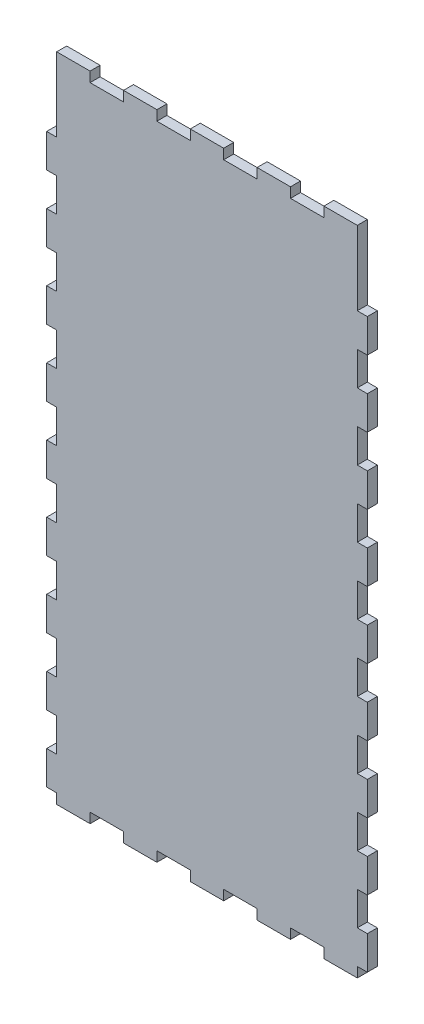
SolidWorks part; units mm, degrees
ref_plane "Plan de face" through (0, 0, 0) normal (0, 0, 1) x (1, 0, 0)
ref_plane "Plan de dessus" through (0, 0, 0) normal (0, 1, 0) x (1, 0, 0)
ref_plane "Plan de droite" through (0, 0, 0) normal (1, 0, 0) x (0, 0, -1)
sketch "Esquisse1" plane through (0, 0, 0) normal (0, 0, 1) x (1, 0, 0)
  line L1 (0, 0) -> (90, 0)
  line L2 (0, 0) -> (0, -189.15)
  line L3 (0, -189.15) -> (90, -189.15)
  line L4 (90, 0) -> (90, -189.15)
  dimension "D1" = 90
  dimension "D2" = 189.15
extrude "Boss.-Extru.1" add sketch "Esquisse1" along normal blind 3
sketch "Esquisse2" plane through (0, 0, 0) normal (0, 1, 0) x (1, 0, 0)
  line L0 (90, -3) -> (0, -3) construction
  line L1 (0, 0) -> (10, 0)
  line L2 (0, 0) -> (0, -3)
  line L3 (0, -3) -> (10, -3)
  line L4 (10, 0) -> (10, -3)
  dimension "D1" = 10
extrude "Boss.-Extru.2" add sketch "Esquisse2" along normal blind 3
pattern_linear "Répétition linéaire1" count 5 spacing 20 along (1, 0, 0) of "Boss.-Extru.2"
sketch "Esquisse3" plane through (0, -189.15, 0) normal (0, -1, 0) x (1, 0, 0)
  line L0 (0, 0) -> (90, 0) construction
  line L1 (0, 3) -> (10, 3)
  line L2 (0, 3) -> (0, 0)
  line L3 (0, 0) -> (10, 0)
  line L4 (10, 3) -> (10, 0)
  dimension "D1" = 10
extrude "Boss.-Extru.3" add sketch "Esquisse3" along normal blind 3
pattern_linear "Répétition linéaire2" count 5 spacing 20 along (1, 0, 0) of "Boss.-Extru.3"
sketch "Esquisse4" plane through (0, 0, 0) normal (-1, 0, 0) x (0, 0, 1)
  line L0 (3, 3) -> (3, -192.15) construction
  line L1 (3, -179.15) -> (0, -179.15)
  line L2 (3, -179.15) -> (3, -189.15)
  line L3 (3, -189.15) -> (0, -189.15)
  line L4 (0, -179.15) -> (0, -189.15)
  line L5 (0, 3) -> (0, -192.15) construction
  line L7 (3, -192.15) -> (0, -192.15) construction
  dimension "D1" = 10
  dimension "D2" = 3
extrude "Boss.-Extru.4" add sketch "Esquisse4" along normal blind 3
pattern_linear "Répétition linéaire3" count 9 spacing 20 along (0, 1, 0) of "Boss.-Extru.4"
sketch "Esquisse5" plane through (90, 0, 0) normal (1, 0, 0) x (0, 0, -1)
  line L0 (-3, -192.15) -> (-3, 3) construction
  line L1 (-3, -189.15) -> (0, -189.15)
  line L2 (-3, -189.15) -> (-3, -179.15)
  line L3 (-3, -179.15) -> (0, -179.15)
  line L4 (0, -189.15) -> (0, -179.15)
  line L5 (0, -192.15) -> (0, 3) construction
  line L8 (0, -192.15) -> (-3, -192.15) construction
  dimension "D1" = 10
  dimension "D2" = 3
extrude "Boss.-Extru.5" add sketch "Esquisse5" along normal blind 3
pattern_linear "Répétition linéaire4" count 9 spacing 20 along (0, 1, 0) of "Boss.-Extru.5"
